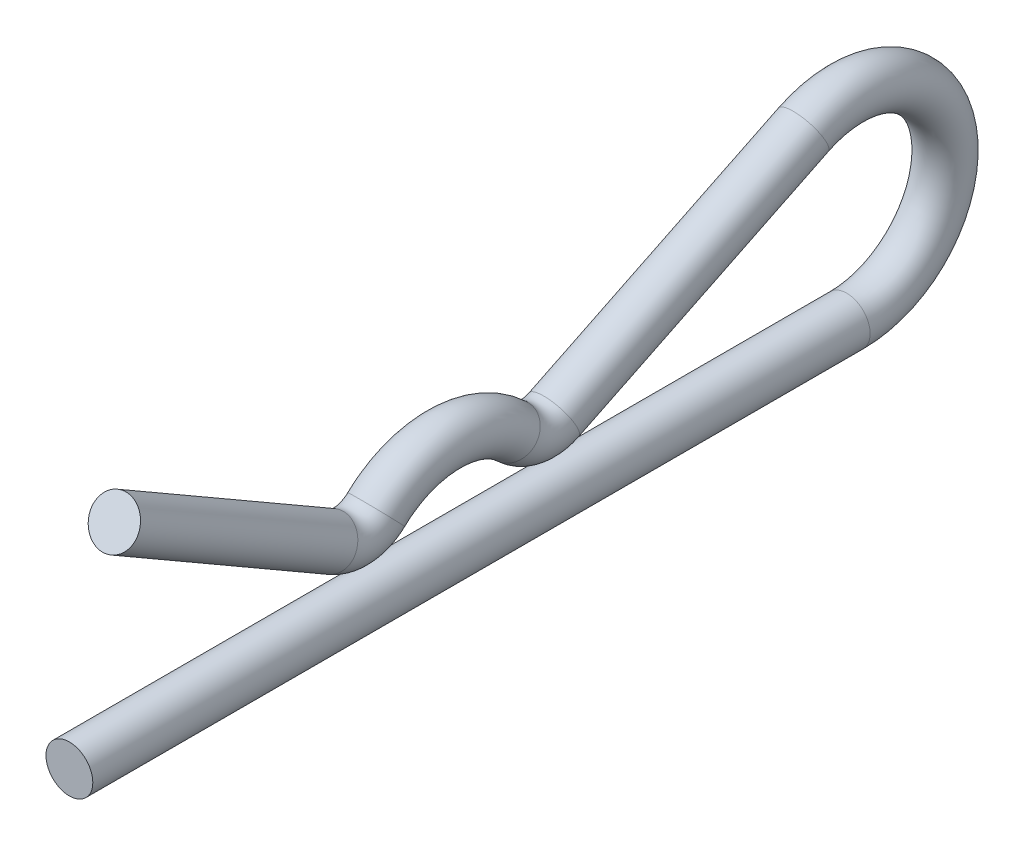
SolidWorks part; units mm, degrees
ref_plane "Front" through (0, 0, 0) normal (0, 0, 1) x (1, 0, 0)
ref_plane "Top" through (0, 0, 0) normal (0, 1, 0) x (1, 0, 0)
ref_plane "Right" through (0, 0, 0) normal (1, 0, 0) x (0, 0, -1)
sketch "Sketch1" plane through (0, 0, 0) normal (0, 0, 1) x (1, 0, 0)
  circle A0 centre (0, 0) radius 0.9922
sketch "Sketch2" plane through (0, 0, 0) normal (1, 0, 0) x (0, 0, -1)
  line L0 (0, 0) -> (32.9406, 0)
  line L1 (11.9062, 4.1672) -> (19.8438, 4.1672) construction
  line L2 (38.1, 0) -> (38.1, 4.1672) construction
  line L3 (38.1, 4.1672) -> (37.1078, 4.1672) construction
  line L5 (38.1, 0) -> (0, 0) construction
  line L6 (11.1125, 2.7924) -> (1.905, 8.1083)
  line L7 (15.875, 4.1672) -> (15.875, 0) construction
  line L13 (31.1096, 7.9105) -> (20.5413, 2.7411)
  circle A0 centre (32.9406, 4.1672) radius 3.175 construction
  arc A1 (18.7489, 3.0176) -> (13.0011, 3.0176) centre (15.875, 0) ccw
  arc A6 (13.0011, 3.0176) -> (11.1125, 2.7924) centre (11.9062, 4.1672) cw
  arc A8 (20.5413, 2.7411) -> (18.7489, 3.0176) centre (19.8438, 4.1672) cw
  arc A9 (32.9406, 0) -> (31.1096, 7.9105) centre (32.9406, 4.1672) ccw
  dimension "D1" = 1.5875
  dimension "D2" = 15.875
  dimension "D5" = 1.905
  dimension "D9" = 30
  dimension "D11" = 0.9922
  dimension "D3" = 0.9922
sweep "Sweep1" add profiles "Sketch1" path "Sketch2"
equation "\"D11@Sketch2\" = \"WireOD@Sketch1\"/2"
equation "\"D1@Sketch2\" = \"EyeID@Sketch2\"/4"
equation "\"D3@Sketch2\" = \"D11@Sketch2\""
equation "\"D2@Sketch2\" = (\"Length@Sketch2\"-\"EyeID@Sketch2\")/2"
equation "\"D5@Sketch2\" = \"Length@Sketch2\"*.05"
